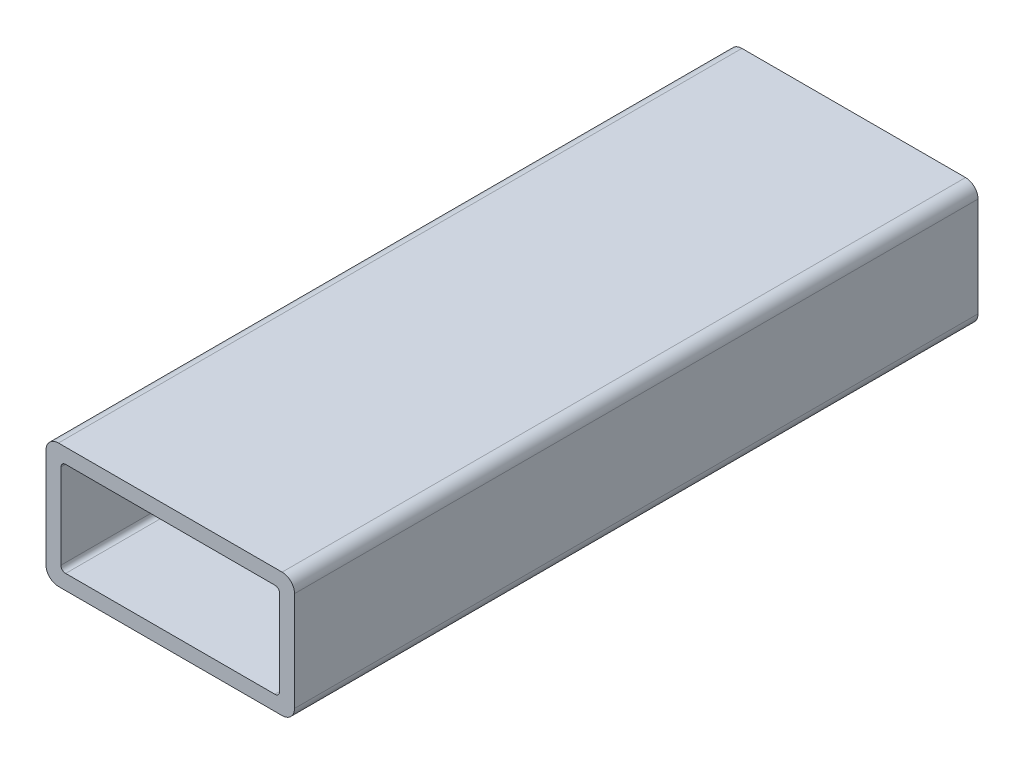
SolidWorks part; units mm, degrees
ref_plane "Front" through (0, 0, 0) normal (0, 0, 1) x (1, 0, 0)
ref_plane "Top" through (0, 0, 0) normal (0, 1, 0) x (1, 0, 0)
ref_plane "Right" through (0, 0, 0) normal (1, 0, 0) x (0, 0, -1)
sketch "Sketch1" plane through (0, 0, 0) normal (0, 0, 1) x (1, 0, 0)
  line L0 (-22.352, 0) -> (-25.4, 0) construction
  line L1 (22.86, -12.7) -> (-22.86, -12.7)
  line L2 (25.4, -10.16) -> (25.4, 10.16)
  line L3 (22.86, 12.7) -> (-22.86, 12.7)
  line L4 (-25.4, -10.16) -> (-25.4, 10.16)
  line L5 (25.4, -12.7) -> (-25.4, 12.7) construction
  line L6 (25.4, 12.7) -> (-25.4, -12.7) construction
  line L7 (21.3868, 9.652) -> (-21.3868, 9.652)
  line L8 (22.352, 8.6868) -> (22.352, -8.6868)
  line L9 (21.3868, -9.652) -> (-21.3868, -9.652)
  line L10 (-22.352, 8.6868) -> (-22.352, -8.6868)
  line L11 (22.352, 9.652) -> (-22.352, -9.652) construction
  line L12 (22.352, -9.652) -> (-22.352, 9.652) construction
  line L13 (0, -9.652) -> (0, -12.7) construction
  line L14 (22.352, -8.6868) -> (22.352, -12.7) construction
  line L16 (22.352, -12.7) -> (25.4, -12.7) construction
  arc A0 (-21.3868, -9.652) -> (-22.352, -8.6868) centre (-21.3868, -8.6868) cw
  arc A1 (22.352, -8.6868) -> (21.3868, -9.652) centre (21.3868, -8.6868) cw
  arc A2 (21.3868, 9.652) -> (22.352, 8.6868) centre (21.3868, 8.6868) cw
  arc A3 (-21.3868, 9.652) -> (-22.352, 8.6868) centre (-21.3868, 8.6868) ccw
  arc A4 (22.86, -12.7) -> (25.4, -10.16) centre (22.86, -10.16) ccw
  arc A5 (25.4, 10.16) -> (22.86, 12.7) centre (22.86, 10.16) ccw
  arc A6 (-22.86, 12.7) -> (-25.4, 10.16) centre (-22.86, 10.16) ccw
  arc A7 (-22.86, -12.7) -> (-25.4, -10.16) centre (-22.86, -10.16) cw
  point P0 (0, 0)
  point P6 (0, 0)
  dimension "D2" = 0.9652
  dimension "D3" = 2.54
sketch "Sketch2" plane through (0, 0, 0) normal (1, 0, 0) x (0, 0, -1)
  line L0 (-152.4, 0) -> (152.4, 0) construction
  dimension "Length" = 304.8
ref_plane "Plane1" through (25.4, 0, 0) normal (1, 0, 0) x (0, 0, -1)
sketch "Sketch5" plane through (25.4, 0, 0) normal (1, 0, 0) x (0, 0, -1)
  line L0 (-152.4, 12.7) -> (-152.4, -12.7) construction
  line L1 (152.4, 12.7) -> (152.4, -12.7) construction
sketch "Sketch4" plane through (0, 0, 0) normal (0, 0, 1) x (1, 0, 0)
  line L0 (25.4, -10.16) -> (25.4, 10.16) construction
  line L1 (22.86, 12.7) -> (-22.86, 12.7) construction
  line L2 (-25.4, -10.16) -> (-25.4, 10.16) construction
  line L3 (22.86, -12.7) -> (-22.86, -12.7) construction
  line L4 (22.352, 8.6868) -> (22.352, -8.6868) construction
  line L5 (21.3868, -9.652) -> (-21.3868, -9.652) construction
  line L6 (-22.352, 8.6868) -> (-22.352, -8.6868) construction
  line L7 (21.3868, 9.652) -> (-21.3868, 9.652) construction
  line L8 (25.4, -10.16) -> (25.4, 10.16)
  line L9 (22.86, 12.7) -> (-22.86, 12.7)
  line L10 (-25.4, -10.16) -> (-25.4, 10.16)
  line L11 (22.86, -12.7) -> (-22.86, -12.7)
  line L12 (22.352, 8.6868) -> (22.352, -8.6868)
  line L13 (21.3868, -9.652) -> (-21.3868, -9.652)
  line L14 (-22.352, 8.6868) -> (-22.352, -8.6868)
  line L15 (21.3868, 9.652) -> (-21.3868, 9.652)
  arc A0 (25.4, 10.16) -> (22.86, 12.7) centre (22.86, 10.16) ccw construction
  arc A1 (-22.86, 12.7) -> (-25.4, 10.16) centre (-22.86, 10.16) ccw construction
  arc A2 (-25.4, -10.16) -> (-22.86, -12.7) centre (-22.86, -10.16) ccw construction
  arc A3 (22.86, -12.7) -> (25.4, -10.16) centre (22.86, -10.16) ccw construction
  arc A4 (21.3868, -9.652) -> (22.352, -8.6868) centre (21.3868, -8.6868) ccw construction
  arc A5 (-22.352, -8.6868) -> (-21.3868, -9.652) centre (-21.3868, -8.6868) ccw construction
  arc A6 (-21.3868, 9.652) -> (-22.352, 8.6868) centre (-21.3868, 8.6868) ccw construction
  arc A7 (22.352, 8.6868) -> (21.3868, 9.652) centre (21.3868, 8.6868) ccw construction
  arc A8 (25.4, 10.16) -> (22.86, 12.7) centre (22.86, 10.16) ccw
  arc A9 (-22.86, 12.7) -> (-25.4, 10.16) centre (-22.86, 10.16) ccw
  arc A10 (-25.4, -10.16) -> (-22.86, -12.7) centre (-22.86, -10.16) ccw
  arc A11 (22.86, -12.7) -> (25.4, -10.16) centre (22.86, -10.16) ccw
  arc A12 (21.3868, -9.652) -> (22.352, -8.6868) centre (21.3868, -8.6868) ccw
  arc A13 (-22.352, -8.6868) -> (-21.3868, -9.652) centre (-21.3868, -8.6868) ccw
  arc A14 (-21.3868, 9.652) -> (-22.352, 8.6868) centre (-21.3868, 8.6868) ccw
  arc A15 (22.352, 8.6868) -> (21.3868, 9.652) centre (21.3868, 8.6868) ccw
extrude "Boss-Extrude1" add sketch "Sketch4" along normal blind 139.7
sketch "Sketch6" plane through (0, 12.7, 0) normal (0, 1, 0) x (1, 0, 0)
  line L0 (0, -139.7) -> (0, 0) construction
  line L1 (22.86, -139.7) -> (-22.86, -139.7) construction
  line L2 (22.86, 0) -> (-22.86, 0) construction
  line L3 (-22.86, -69.85) -> (22.86, -69.85) construction
  line L4 (-22.86, 0) -> (-22.86, -139.7) construction
  line L5 (22.86, 0) -> (22.86, -139.7) construction
equation "\"D3@Sketch1\"=\"Outside Width@Sketch1\"*.05"
equation "\"D2@Sketch1\"=\"D1@Sketch1\"*.05"
